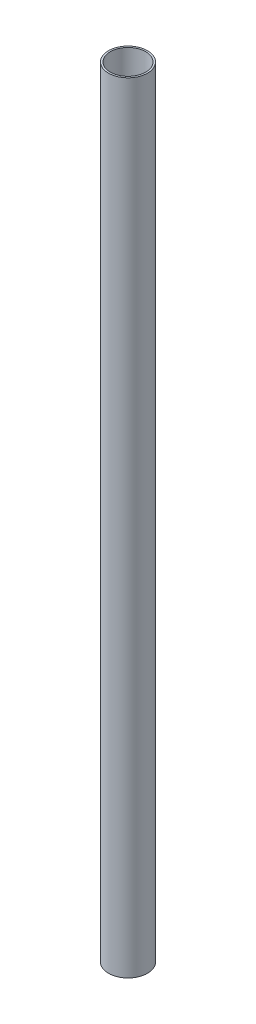
SolidWorks part; units mm, degrees
ref_plane "Front Plane" through (0, 0, 0) normal (0, 0, 1) x (1, 0, 0)
ref_plane "Top Plane" through (0, 0, 0) normal (0, 1, 0) x (1, 0, 0)
ref_plane "Right Plane" through (0, 0, 0) normal (1, 0, 0) x (0, 0, -1)
sketch "Sketch1" plane through (0, 0, 0) normal (0, 1, 0) x (1, 0, 0)
  circle A0 centre (0, 0) radius 11
  circle A1 centre (0, 0) radius 10
  dimension "D1" = 22
  dimension "D2" = 1
extrude "Extrude1" add sketch "Sketch1" along normal mid plane 440
